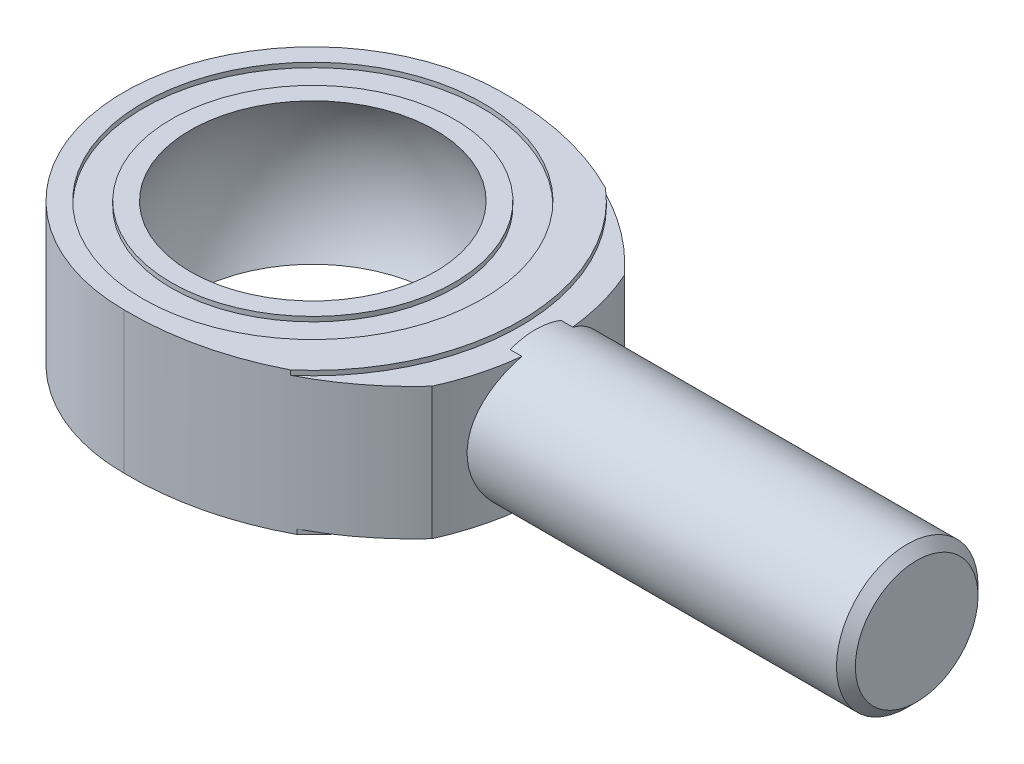
SolidWorks part; units mm, degrees
ref_plane "Front Plane" through (0, 0, 0) normal (0, 0, 1) x (1, 0, 0)
ref_plane "Top Plane" through (0, 0, 0) normal (0, 1, 0) x (1, 0, 0)
ref_plane "Right Plane" through (0, 0, 0) normal (1, 0, 0) x (0, 0, -1)
sketch "Sketch2" plane through (0, 0, 0) normal (0, 1, 0) x (1, 0, 0)
  circle A1 centre (0, 0) radius 15.875
extrude "Boss-Extrude1" add sketch "Sketch2" along normal blind 8.89
sketch "Sketch3" plane through (0, 8.89, 0) normal (0, 1, 0) x (1, 0, 0)
  circle A0 centre (0, 0) radius 12.7
  circle A1 centre (0, 0) radius 13.97
extrude "Boss-Extrude2" add sketch "Sketch3" along normal blind 0.3175 contours A1
sketch "Sketch4" plane through (0, 0, 0) normal (0, -1, 0) x (-1, 0, 0)
  circle A0 centre (0, 0) radius 12.7
  circle A1 centre (0, 0) radius 14.0462
extrude "Boss-Extrude3" add sketch "Sketch4" along normal blind 0.3175 contours A1
sketch "Sketch5" plane through (0, -0.3175, 0) normal (0, -1, 0) x (-1, 0, 0)
  line L0 (-15.875, 4.7625) -> (-15.875, -4.7625)
  circle A0 centre (0, 0) radius 12.7
  circle A1 centre (0, 0) radius 15.875
  arc A2 (-15.875, 4.7625) -> (0, 12.7) centre (-0.399, -6.3458) cw
  arc A3 (-15.875, -4.7625) -> (0, -12.7) centre (-0.399, 6.3458) ccw
  point P7 (-15.875, 0)
  circle M4 centre (0, 0) radius 14.0462
extrude "Cut-Extrude2" cut sketch "Sketch5" against normal through all contours A3 A1 A2 M4 | A3 A2 A0 M4
sketch "Sketch6" plane through (0, 0, 0) normal (1, 0, 0) x (0, 0, -1)
  line L0 (0, 0) -> (0, 4.445)
  line L1 (0, -5.08) -> (0, 13.97)
  arc A0 (0, 13.97) -> (0, -5.08) centre (0, 4.445) ccw
  point P7 (0, 4.445)
revolve "Cut-Revolve1" cut sketch "Sketch6" angle 360 about L1
sketch "Sketch7" plane through (0, 9.2075, 0) normal (0, 1, 0) x (1, 0, 0)
  circle A0 centre (0, 0) radius 9.525
  circle A1 centre (0, 0) radius 11.43
extrude "Cut-Extrude3" cut sketch "Sketch7" against normal blind 0.3175
ref_plane "Plane1" through (15.24, 0, 0) normal (1, 0, 0) x (0, 0, -1)
sketch "Sketch9" plane through (15.24, 0, 0) normal (1, 0, 0) x (0, 0, -1)
  line L0 (0, 0) -> (0, 4.445)
  circle A0 centre (0, 4.445) radius 4.7625
extrude "Boss-Extrude4" add sketch "Sketch9" along normal blind 25.4 and the other way blind 0.254
sketch "Sketch11" plane through (0, 0, 0) normal (0, 0, 1) x (1, 0, 0)
  line L0 (40.64, 4.445) -> (40.64, -0.3175)
  line L2 (40.64, -0.3175) -> (39.37, -0.3175)
  line L4 (14.986, -0.3175) -> (40.64, -0.3175) construction
  line L5 (40.005, -0.3175) -> (40.64, 0.3175)
  line L6 (40.64, -0.3175) -> (40.64, 9.2075) construction
  line L7 (40.64, 4.445) -> (21.59, 4.445)
revolve "Cut-Revolve2" cut sketch "Sketch11" angle 360 about L7
sketch3d "3DSketch1"
  line L0 (0, 8.89, 0) -> (0, 0, 0)
